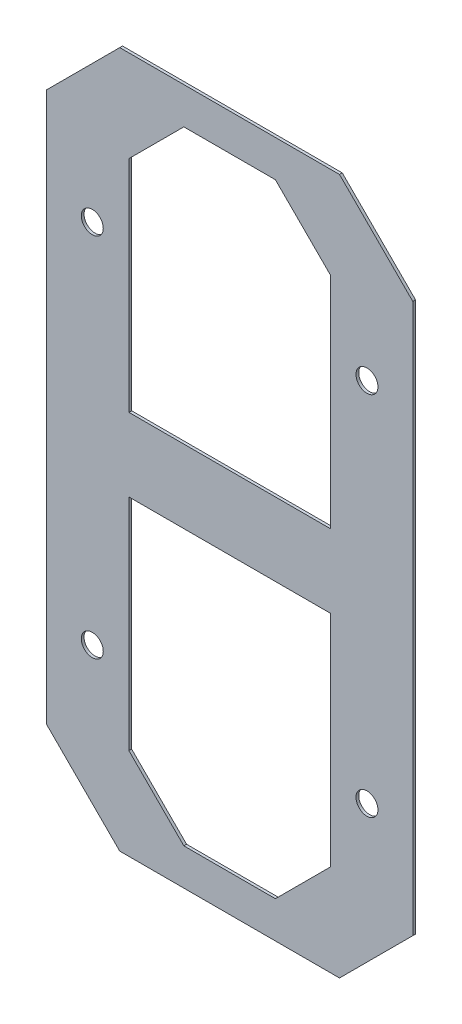
SolidWorks part; units mm, degrees
material "PE High Density"
ref_plane "Front Plane" through (0, 0, 0) normal (0, 0, 1) x (1, 0, 0)
ref_plane "Top Plane" through (0, 0, 0) normal (0, 1, 0) x (1, 0, 0)
ref_plane "Right Plane" through (0, 0, 0) normal (1, 0, 0) x (0, 0, -1)
sketch "Sketch1" plane through (0, 0, 0) normal (0, 0, 1) x (1, 0, 0)
  line L1 (-254, 482.6) -> (254, 482.6)
  line L2 (-254, 482.6) -> (-254, -482.6)
  line L3 (-254, -482.6) -> (254, -482.6)
  line L4 (254, 482.6) -> (254, -482.6)
  line L5 (-254, 482.6) -> (254, -482.6) construction
  line L6 (-254, -482.6) -> (254, 482.6) construction
  point P1 (0, 0)
  point P6 (0, 0)
  dimension "D1" = 965.2
  dimension "D2" = 508
extrude "Boss-Extrude1" add sketch "Sketch1" along normal blind 3.81 contours L2 L3 L4 L1
hole_wizard "1/16 (1.2) Diameter Hole1" positions "Sketch2" profile "Sketch3" hole size "1/16" standard "ANSI Inch" end condition through all
sketch "Sketch2" plane through (0, 0, 3.81) normal (0, 0, 1) x (1, 0, 0)
  line L0 (-190.5, 254) -> (190.5, 254) construction
  line L1 (190.5, 254) -> (190.5, -254) construction
  line L2 (190.5, -254) -> (-190.5, -254) construction
  line L3 (-190.5, -254) -> (-190.5, 254) construction
  point P0 (-190.5, 254)
  point P2 (190.5, 254)
  point P4 (190.5, -254)
  point P6 (-190.5, -254)
  point P20 (-190.5, 0)
  point P22 (0, 254)
  dimension "D1" = 381
  dimension "D2" = 508
sketch "Sketch3" plane through (-190.5, 254, 3.81) normal (1, 0, 0) x (0, -1, 0)
  line L0 (0, 0) -> (0, 3.81)
  line L1 (0, 3.81) -> (15.24, 3.81)
  line L2 (15.24, 3.81) -> (15.24, 0)
  line L5 (15.24, 0) -> (0, 0)
  line L11 (0, -6.35) -> (0, 107.95) construction
  dimension "Thru Hole Dia." = 30.48
  dimension "Thru Hole Depth" = 3.81
chamfer "Chamfer1" distance 101.6 angle 45 4 edges at (-254, 482.6, 1.905) (254, 482.6, 1.905) (254, -482.6, 1.905) (-254, -482.6, 1.905)
sketch "Sketch6" plane through (0, 0, 3.81) normal (0, 0, 1) x (1, 0, 0)
  line L0 (254, 381) -> (254, -381) construction
  line L1 (-63.5, 431.8) -> (63.5, 431.8)
  line L2 (-139.7, 355.6) -> (-139.7, 50.8)
  line L3 (-139.7, 50.8) -> (139.7, 50.8)
  line L4 (139.7, 355.6) -> (139.7, 50.8)
  line L5 (-139.7, 431.8) -> (139.7, 50.8) construction
  line L6 (-139.7, 50.8) -> (139.7, 431.8) construction
  line L7 (-254, 381) -> (-254, -381) construction
  line L8 (-152.4, 482.6) -> (152.4, 482.6) construction
  line L9 (141.7955, 0) -> (-141.7955, 0) construction
  line L10 (-139.7, -50.8) -> (139.7, -431.8) construction
  line L11 (-139.7, -431.8) -> (139.7, -50.8) construction
  line L12 (139.7, -355.6) -> (139.7, -50.8)
  line L13 (-139.7, -50.8) -> (139.7, -50.8)
  line L14 (-139.7, -355.6) -> (-139.7, -50.8)
  line L15 (-63.5, -431.8) -> (63.5, -431.8)
  line L17 (63.5, 431.8) -> (139.7, 355.6)
  line L18 (-139.7, 355.6) -> (-63.5, 431.8)
  line L19 (-63.5, -431.8) -> (-139.7, -355.6)
  line L20 (63.5, -431.8) -> (139.7, -355.6)
  point P0 (0, 241.3)
  point P18 (0, -241.3)
  point P25 (-139.7, 431.8)
  dimension "D1" = 50.8
  dimension "D2" = 114.3
  dimension "D3" = 114.3
  dimension "D4" = 50.8
extrude "Cut-Extrude2" cut sketch "Sketch6" against normal through all
